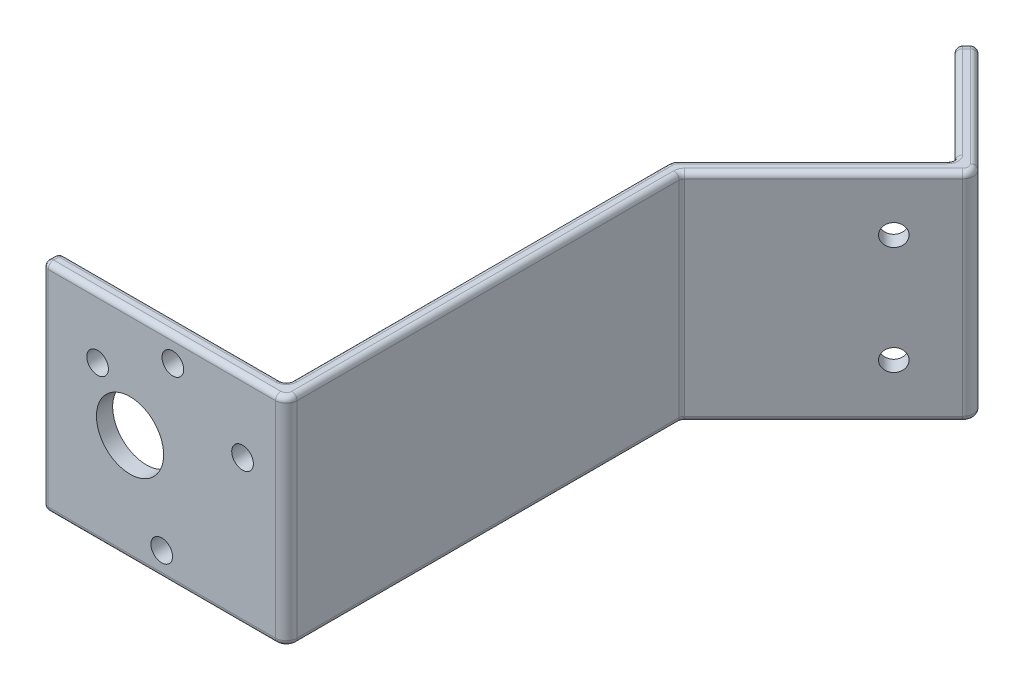
SolidWorks part; units mm, degrees
ref_plane "Front Plane" through (0, 0, 0) normal (0, 0, 1) x (1, 0, 0)
ref_plane "Top Plane" through (0, 0, 0) normal (0, 1, 0) x (1, 0, 0)
ref_plane "Right Plane" through (0, 0, 0) normal (1, 0, 0) x (0, 0, -1)
sketch "FixedMotor" plane through (0, 0, 0) normal (0, 0, 1) x (1, 0, 0)
  line L0 (-6.8841, 0) -> (0, 0) construction
  line L1 (0, 0) -> (48.2205, 0) construction
  line L2 (-6.8841, 0) -> (-54.875, 0) construction
  line L3 (-23, 0) -> (-23, -20)
  line L4 (-23, 0) -> (-23, 20)
  line L5 (-23, -20) -> (19, -20)
  line L6 (-23, 20) -> (19, 20)
  line L7 (19, 20) -> (19, -20)
  circle A0 centre (0, 0) radius 18.5 construction
  circle A1 centre (1.0291, 15.4658) radius 2
  circle A2 centre (13.9083, 6.8417) radius 2
  circle A3 centre (-12.8792, 8.6241) radius 2
  circle A4 centre (-1.0291, -15.4658) radius 2
  circle A5 centre (-6.8417, 13.9083) radius 2 construction
  circle A6 centre (-8.6241, -12.8792) radius 2 construction
  circle A7 centre (15.4658, -1.0291) radius 2 construction
  circle A8 centre (-6.8841, 0) radius 6.207
  circle A9 centre (-6.8841, 0) radius 3.0239
  point P16 (-5.9251, 12.045)
  dimension "D1" = 20
  dimension "D2" = 20
  dimension "D4" = 42
  dimension "D5" = 23
  dimension "D3" = 42
extrude "Boss-Extrude1" add sketch "FixedMotor" along normal blind 3 contours L7 L6 L4 L3 L5 A8 A4 A3 A2 A1
sketch "Sketch2" plane through (19, 0, 0) normal (1, 0, 0) x (0, 0, -1)
  line L0 (0, 20) -> (70, 20)
  line L1 (0, -20) -> (70, -20)
  line L2 (70, -20) -> (70, 20)
  line L7 (0, -20) -> (0, 20)
  line L8 (0, 20) -> (-3, 20)
  line L9 (-3, 20) -> (-3, -20)
  line L10 (-3, -20) -> (0, -20)
  line L12 (0, 20) -> (-3, 20)
  line L13 (-3, 20) -> (-3, -20)
  line L14 (-3, -20) -> (0, -20)
  dimension "D1" = 70
  dimension "D2" = 0
extrude "Boss-Extrude2" add sketch "Sketch2" along normal blind 3
fillet "Fillet2" radius 1 1 edges
fillet "Fillet3" radius 2 1 edges at (22, 0, 3)
fillet "Fillet4" radius 1 1 edges at (-23, 0, 3)
fillet "Fillet5" radius 1 1 edges at (-23, 0, 0)
sketch "Sketch5" plane through (0, -20, 0) normal (0, -1, 0) x (1, 0, 0)
  line L0 (22, -70) -> (19, -67)
  line L1 (19, -1) -> (19, -70) construction
  line L2 (19, -67) -> (19, -70)
  line L3 (19, -70) -> (22, -70)
  dimension "D1" = 3
extrude "Cut-Extrude1" cut sketch "Sketch5" against normal blind 40
sketch "Sketch6" plane through (-24, 0, -24) normal (-0.7071, 0, -0.7071) x (-0.7071, 0, 0.7071)
  line L0 (-60.8112, 20) -> (-100.8112, 20)
  line L1 (-60.8112, -20) -> (-100.8112, -20)
  line L2 (-100.8112, -20) -> (-100.8112, 20)
  line L7 (-65.0538, -20) -> (-60.8112, -20)
  line L8 (-60.8112, -20) -> (-60.8112, 20)
  line L9 (-60.8112, 20) -> (-65.0538, 20)
  line L10 (-65.0538, 20) -> (-65.0538, -20)
  line L11 (-65.0538, -20) -> (-60.8112, -20)
  line L13 (-60.8112, 20) -> (-65.0538, 20)
  line L14 (-65.0538, 20) -> (-65.0538, -20)
  line M6 (-65.0538, -20) -> (-60.8112, -20)
  line M7 (-60.8112, -20) -> (-60.8112, 20)
  line M8 (-60.8112, 20) -> (-65.0538, 20)
  line M9 (-65.0538, 20) -> (-65.0538, -20)
  dimension "D1" = 40
  dimension "D2" = 0
extrude "Boss-Extrude3" add sketch "Sketch6" along normal blind 3 contours L2 L1 L0 M9 | M9 M6 M7 M8
sketch "Sketch7" plane through (0, 20, 0) normal (0, 1, 0) x (1, 0, 0)
  line L0 (19, 67) -> (19, 71.2426)
  line L1 (16.8787, 69.1213) -> (45.163, 97.4056) construction
  line L2 (19, 71.2426) -> (16.8787, 69.1213)
  line L3 (16.8787, 69.1213) -> (19, 67)
extrude "Cut-Extrude2" cut sketch "Sketch7" against normal up to vertex (40 mm away)
fillet "Fillet6" radius 2 1 edges at (19, 0, -71.2426)
fillet "Fillet7" radius 1 1 edges at (22, 0, -70)
sketch "Sketch8" plane through (71.2843, 0, -71.2843) normal (0.7071, 0, -0.7071) x (-0.7071, 0, -0.7071)
  line L0 (33.9411, 20) -> (63.9411, 20)
  line L1 (33.9411, -20) -> (63.9411, -20)
  line L2 (63.9411, -20) -> (63.9411, 20)
  line L3 (33.9411, 20) -> (33.9411, -20)
  dimension "D1" = 30
extrude "Boss-Extrude4" add sketch "Sketch8" along normal blind 3
fillet "Fillet8" radius 2 1 edges at (49.4056, 0, -97.4056)
fillet "Fillet9" radius 1 1 edges at (45.163, 0, -97.4056)
sketch "Sketch9" plane through (73.4056, 0, -73.4056) normal (0.7071, 0, -0.7071) x (-0.7071, 0, -0.7071)
  line L0 (63.9411, 0) -> (35.9411, 0) construction
  line L1 (63.9411, -20) -> (63.9411, 20) construction
  line L2 (35.9411, 20) -> (35.9411, -20) construction
  line L3 (43.9411, 0) -> (43.9411, 10) construction
  line L4 (43.9411, 0) -> (43.9411, -10) construction
  circle A0 centre (53.9411, 0) radius 2
  circle A1 centre (43.9411, 10) radius 2
  circle A2 centre (43.9411, -10) radius 2
  point P6 (53.9411, 0)
  point P9 (43.9411, 0)
  dimension "D2" = 4
  dimension "D6" = 4
  dimension "D7" = 4
  dimension "D1" = 10
  dimension "D3" = 10
  dimension "D4" = 10
  dimension "D5" = 10
extrude "Cut-Extrude3" cut sketch "Sketch9" against normal blind 3
fillet "Fillet10" radius 2 1 edges at (27.1317, 20, -117.5581)
fillet "Fillet11" radius 2 1 edges at (27.1317, -20, -117.5581)
fillet "Fillet15" radius 1 40 edges at (26.4853, -19.4142, -116.0833) (35.9706, -20, -106.598) (44.7487, -20, -97.4056) (32.0208, -20, -84.2635) (19.1522, -20, -71.1796) (18.7071, -20, -0.2929) (-22.7071, -20, 0.2929) (-23, -20, 1.5) (-22.7071, -20, 2.7071) (-1, -20, 3) (21.4142, -20, 2.4142) (22, -20, -34.2929) (22.0761, -20, -69.9685) (35.1421, -20, -83.1421) (48.5772, -20, -97.4056) (38.799, -20, -108.0122) (28.6066, -19.4142, -118.2046) (28.1924, 0, -118.6188) (28.6066, 19.4142, -118.2046) (38.799, 20, -108.0122) (48.5772, 20, -97.4056) (35.1421, 20, -83.1421) (22.0761, 20, -69.9685) (22, 20, -34.2929) (21.4142, 20, 2.4142) (-1, 20, 3) (-22.7071, 20, 2.7071) (-23, 20, 1.5) (-22.7071, 20, 0.2929) (18.7071, 20, -0.2929) (19.1522, 20, -71.1796) (32.0208, 20, -84.2635) (44.7487, 20, -97.4056) (35.9706, 20, -106.598) (26.4853, 19.4142, -116.0833) (26.0711, 0, -116.4975)
sketch "Sketch11" plane through (-26.1213, 0, -26.1213) normal (-0.7071, 0, -0.7071) x (-0.7071, 0, 0.7071)
  line L0 (-92.8112, 0) -> (-92.8112, 10) construction
  line L1 (-92.8112, 0) -> (-92.8112, -10) construction
  line L2 (-99.8112, 19) -> (-99.8112, -19) construction
  circle A0 centre (-92.8112, 10) radius 2
  circle A1 centre (-92.8112, -10) radius 2
  dimension "D4" = 4
  dimension "D5" = 4
  dimension "D1" = 10
  dimension "D2" = 10
  dimension "D3" = 7
extrude "Cut-Extrude4" cut sketch "Sketch11" against normal blind 3
